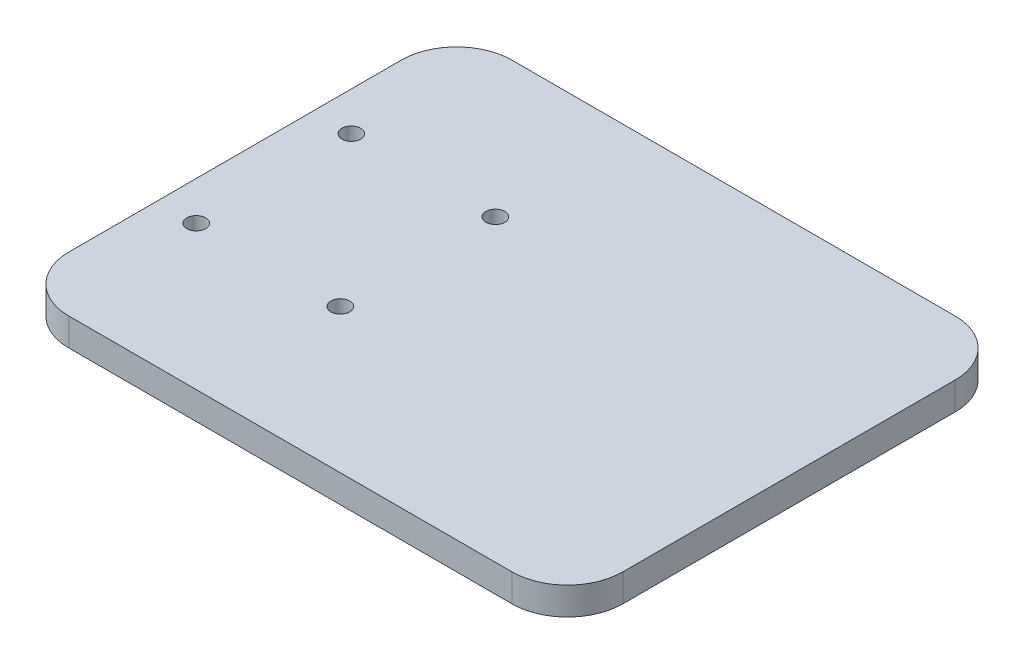
SolidWorks part; units mm, degrees
ref_plane "Front Plane" through (0, 0, 0) normal (0, 0, 1) x (1, 0, 0)
ref_plane "Top Plane" through (0, 0, 0) normal (0, 1, 0) x (1, 0, 0)
ref_plane "Right Plane" through (0, 0, 0) normal (1, 0, 0) x (0, 0, -1)
sketch "Sketch1" plane through (0, 0, 0) normal (0, 1, 0) x (1, 0, 0)
  line L7 (-20, 40) -> (80, 40)
  line L8 (-20, 40) -> (-20, -40)
  line L9 (-20, -40) -> (80, -40)
  line L10 (80, 40) -> (80, -40)
  dimension "D3" = 80
  dimension "D4" = 100
  dimension "D1" = 20
  dimension "D2" = 40
extrude "Boss-Extrude1" add sketch "Sketch1" against normal blind 5 contours L7 L10 L9 L8
sketch "Sketch3" plane through (0, 0, 0) normal (0, 1, 0) x (1, 0, 0)
  line L1 (-13, 14) -> (13, 14) construction
  line L2 (-13, 14) -> (-13, -14) construction
  line L3 (-13, -14) -> (13, -14) construction
  line L4 (13, 14) -> (13, -14) construction
  line L5 (-13, 14) -> (13, -14) construction
  line L6 (-13, -14) -> (13, 14) construction
  point P0 (0, 0)
  dimension "D1" = 26
  dimension "D2" = 28
hole_wizard "M3 Clearance Hole1" positions "3DSketch2" profile "Sketch4" hole size "M3" standard "ISO"
sketch3d "3DSketch2"
  point P0 (-13, 0, -14)
  point P3 (13, 0, -14)
  point P6 (13, 0, 14)
  point P9 (-13, 0, 14)
sketch "Sketch4" plane through (-13, 0, -14) normal (1, 0, 0) x (0, 0, 1)
  line L0 (0, 0) -> (0, 6.0205)
  line L1 (0, 6.0205) -> (1.7, 4.999)
  line L2 (1.7, 4.999) -> (1.7, 0)
  line L5 (1.7, 0) -> (0, 0)
  line L10 (0, 6.0205) -> (-1.7, 4.999) construction
  line L11 (0, -6.35) -> (0, 107.95) construction
  dimension "Hole Dia." = 3.4
  dimension "Hole Depth" = 4.999
  dimension "Drill Angle" = 118
fillet "Fillet1" radius 10 4 edges at (80, -2.5, 40) (80, -2.5, -40) (-20, -2.5, -40) (-20, -2.5, 40)
equation "\"S\"= 26mm'spacing"
equation "\"D1@Sketch3\"=\"S\""
equation "\"W\"= 80mm'width"
equation "\"D3@Sketch1\"=\"W\""
equation "\"D2@Sketch1\"=\"W\"*0.5"
